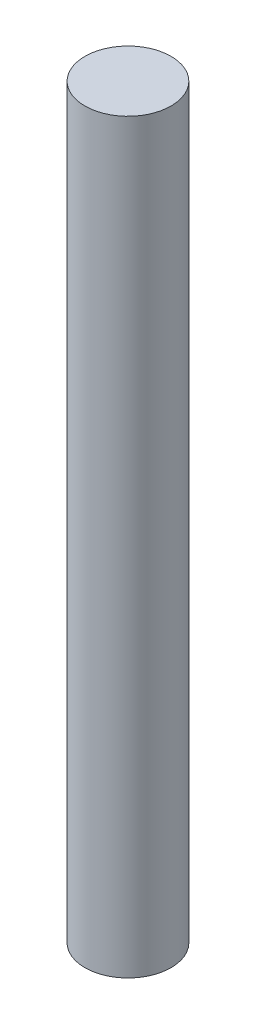
SolidWorks part; units mm, degrees
ref_plane "Front Plane" through (0, 0, 0) normal (0, 0, 1) x (1, 0, 0)
ref_plane "Top Plane" through (0, 0, 0) normal (0, 1, 0) x (1, 0, 0)
ref_plane "Right Plane" through (0, 0, 0) normal (1, 0, 0) x (0, 0, -1)
sketch "Sketch1" plane through (0, 0, 0) normal (0, 1, 0) x (1, 0, 0)
  circle A0 centre (0, 0) radius 0.75
extrude "Boss-Extrude1" add sketch "Sketch1" along normal blind 13
